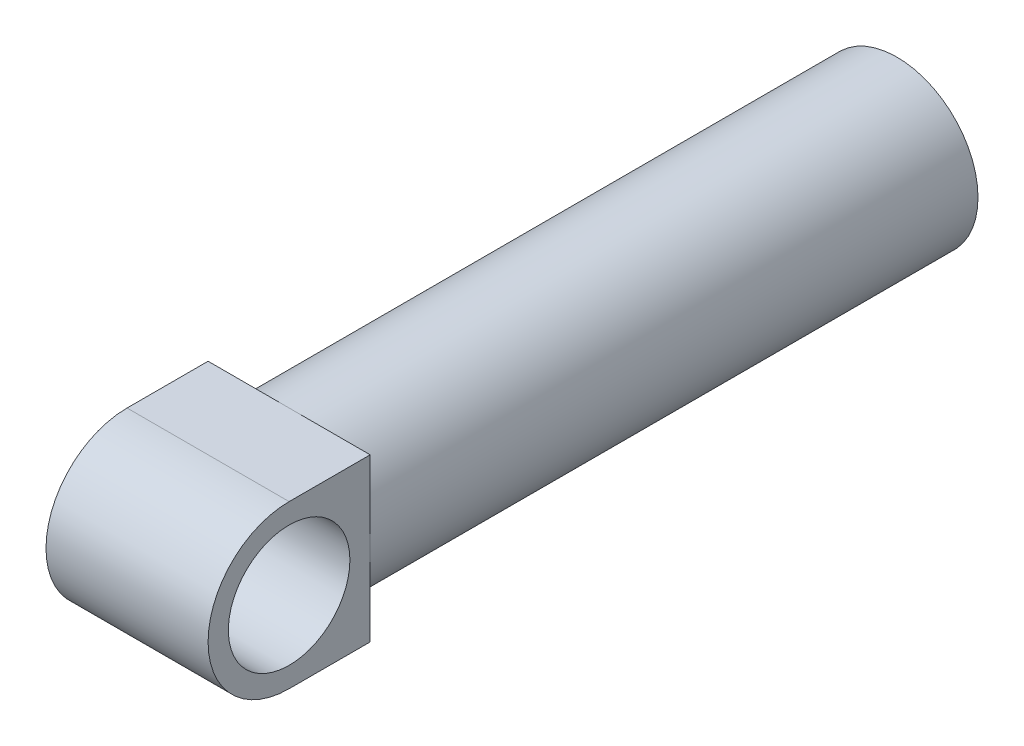
SolidWorks part; units mm, degrees
ref_plane "Płaszczyzna przednia" through (0, 0, 0) normal (0, 0, 1) x (1, 0, 0)
ref_plane "Płaszczyzna górna" through (0, 0, 0) normal (0, 1, 0) x (1, 0, 0)
ref_plane "Płaszczyzna prawa" through (0, 0, 0) normal (1, 0, 0) x (0, 0, -1)
sketch "Szkic1" plane through (0, 0, 0) normal (0, 0, 1) x (1, 0, 0)
  circle A0 centre (0, 0) radius 40
extrude "Dodanie-wyciągnięcie1" add sketch "Szkic1" along normal blind 300
sketch "Szkic2" plane through (0, 0, 0) normal (1, 0, 0) x (0, 0, -1)
  line L2 (-300, 40) -> (-300, -40) construction
  line L3 (0, 40) -> (-300, 40) construction
  line L4 (-340, -40) -> (-300, -40)
  line L5 (-300, -40) -> (-300, 40)
  line L6 (-300, 40) -> (-340, 40)
  arc A2 (-340, 40) -> (-340, -40) centre (-340, 0) ccw
extrude "Dodanie-wyciągnięcie2" add sketch "Szkic2" along normal mid plane 80
sketch "Szkic3" plane through (40, 0, 0) normal (1, 0, 0) x (0, 0, -1)
  circle A0 centre (-340, 0) radius 30
extrude "Wytnij-wyciągnięcie1" cut sketch "Szkic3" against normal through all
